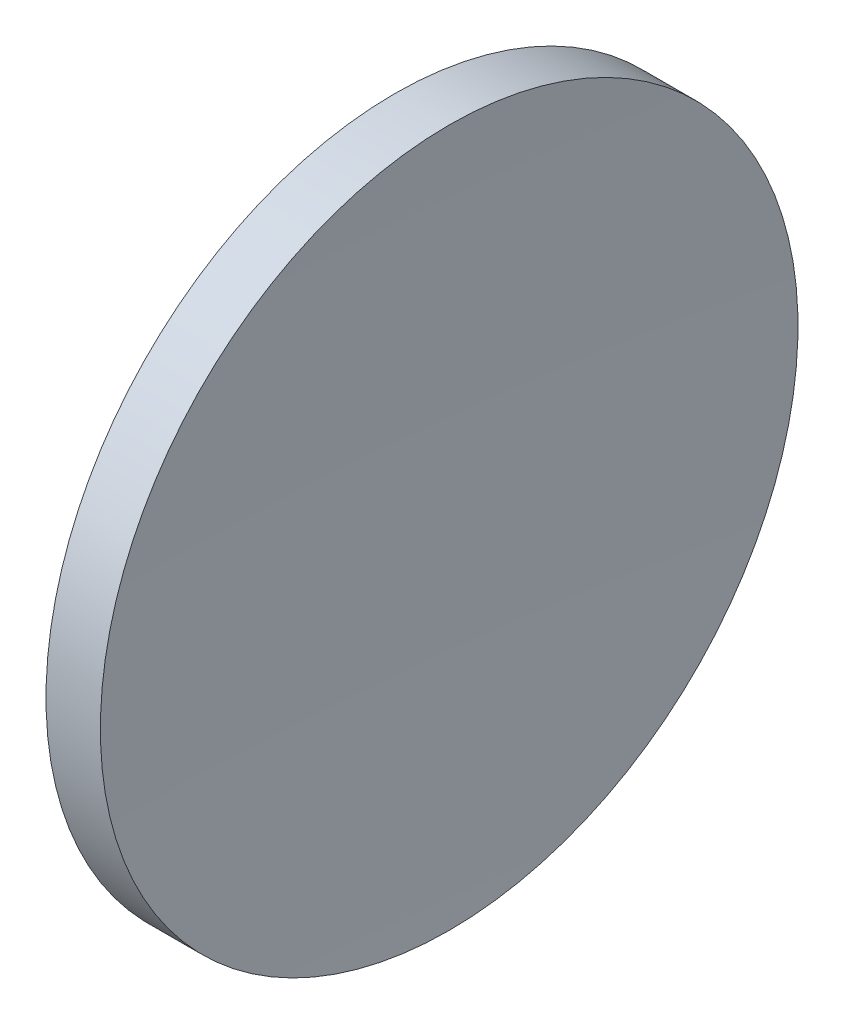
SolidWorks part; units mm, degrees
ref_plane "前视基准面" through (0, 0, 0) normal (0, 0, 1) x (1, 0, 0)
ref_plane "上视基准面" through (0, 0, 0) normal (0, 1, 0) x (1, 0, 0)
ref_plane "右视基准面" through (0, 0, 0) normal (1, 0, 0) x (0, 0, -1)
sketch "草图1" plane through (0, 0, 0) normal (0, 0, 1) x (1, 0, 0)
  line L0 (115.9445, 65.2168) -> (135.9482, 65.2168) construction
  line L1 (124.032, 84.2418) -> (126.9971, 84.2418)
  line L2 (122.8554, 65.2168) -> (126.5554, 65.2168)
  arc A0 (124.032, 84.2418) -> (122.8554, 65.2168) centre (277.2554, 65.2168) ccw
  arc A1 (126.9971, 84.2418) -> (126.5554, 65.2168) centre (536.5554, 65.2168) ccw
  dimension "D2" = 410
  dimension "D3" = 154.4
  dimension "D1" = 2.965
  dimension "D4" = 3.7
revolve "旋转1" add sketch "草图1" angle 360 about L0
